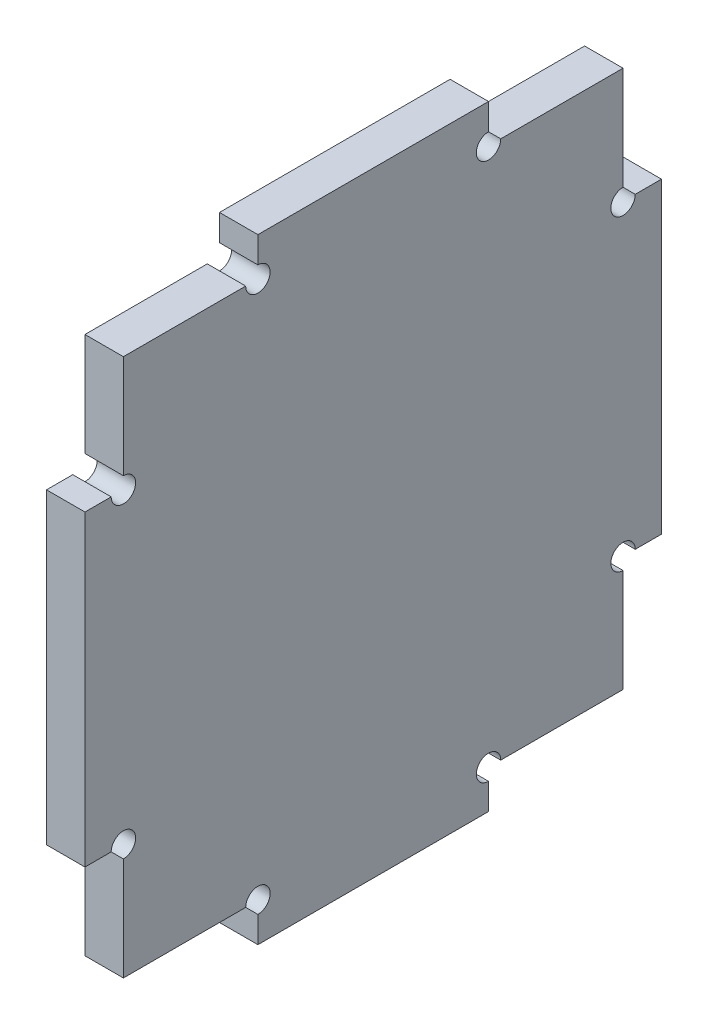
SolidWorks part; units mm, degrees
material "Acrylic (Medium-high impact)"
ref_plane "Front Plane" through (0, 0, 0) normal (0, 0, 1) x (1, 0, 0)
ref_plane "Top Plane" through (0, 0, 0) normal (0, 1, 0) x (1, 0, 0)
ref_plane "Right Plane" through (0, 0, 0) normal (1, 0, 0) x (0, 0, -1)
sketch "Sketch1" plane through (0, 0, 0) normal (1, 0, 0) x (0, 0, -1)
  line L1 (-37.5, -40) -> (37.5, -40)
  line L2 (-37.5, -40) -> (-37.5, 40)
  line L3 (-37.5, 40) -> (37.5, 40)
  line L4 (37.5, -40) -> (37.5, 40)
  line L5 (-37.5, -40) -> (37.5, 40) construction
  line L6 (-37.5, 40) -> (37.5, -40) construction
  point P0 (0, 0)
  dimension "D1" = 75
  dimension "D2" = 80
extrude "Boss-Extrude1" add sketch "Sketch1" along normal blind 5
sketch "Sketch3" plane through (5, 0, 0) normal (1, 0, 0) x (0, 0, -1)
  line L0 (-37.5, 20) -> (-32.5, 20)
  line L1 (-37.5, 40) -> (-37.5, -40) construction
  line L2 (-32.5, 20) -> (-32.5, 35)
  line L3 (-32.5, 35) -> (-15, 35)
  line L4 (-15, 35) -> (-15, 40)
  line L5 (37.5, 40) -> (-37.5, 40) construction
  line L6 (-15, 40) -> (-37.5, 40)
  line L7 (-37.5, 40) -> (-37.5, 20)
  dimension "D1" = 20
  dimension "D2" = 5
  dimension "D3" = 15
extrude "Cut-Extrude1" cut sketch "Sketch3" against normal through all both and the other way through all
mirror "Mirror1" about plane through (0, 0, 0) normal (0, 0, 1) of "Cut-Extrude1" second plane through (0, 0, 0) second plane normal (0, 1, 0)
sketch "Sketch4" plane through (5, 0, 0) normal (1, 0, 0) x (0, 0, -1)
  circle A0 centre (-15, 35) radius 1.5875
  circle A1 centre (15, 35) radius 1.5875
  circle A2 centre (32.5, 20) radius 1.5875
  circle A3 centre (32.5, -20) radius 1.5875
  circle A4 centre (15, -35) radius 1.5875
  circle A5 centre (-15, -35) radius 1.5875
  circle A6 centre (-32.5, -20) radius 1.5875
  circle A7 centre (-32.5, 20) radius 1.5875
  dimension "D1" = 3.175
extrude "Cut-Extrude2" cut sketch "Sketch4" against normal through all
equation "\"cortador\"=3.175"
equation "\"D1@Sketch4\"=\"cortador\""
